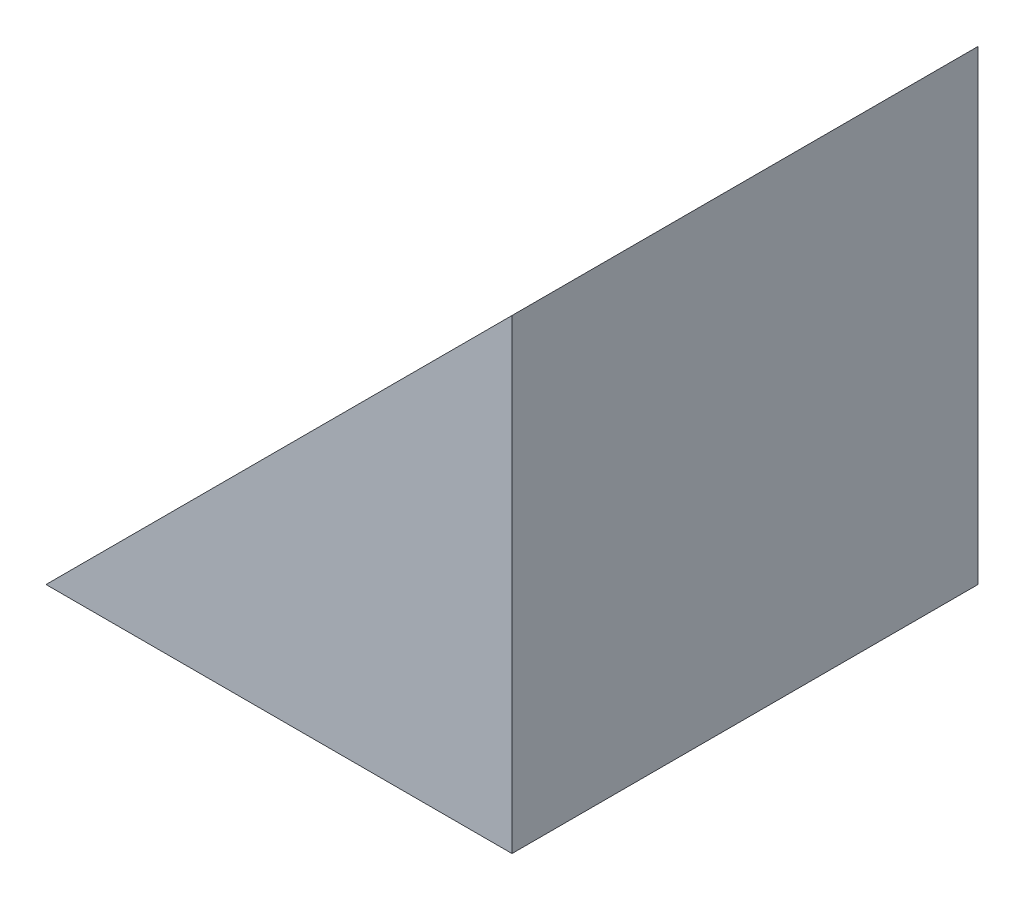
SolidWorks part; units mm, degrees
ref_plane "前视基准面" through (0, 0, 0) normal (0, 0, 1) x (1, 0, 0)
ref_plane "上视基准面" through (0, 0, 0) normal (0, 1, 0) x (1, 0, 0)
ref_plane "右视基准面" through (0, 0, 0) normal (1, 0, 0) x (0, 0, -1)
sketch "草图1" plane through (0, 0, 0) normal (0, 0, 1) x (1, 0, 0)
  line L0 (43.6785, 33.1948) -> (43.6785, 45.6948)
  line L1 (43.6785, 33.1948) -> (31.1785, 33.1948)
  line L2 (31.1785, 33.1948) -> (43.6785, 45.6948)
  dimension "D1" = 12.5
  dimension "D2" = 12.5
extrude "凸台-拉伸1" add sketch "草图1" along normal blind 12.5
